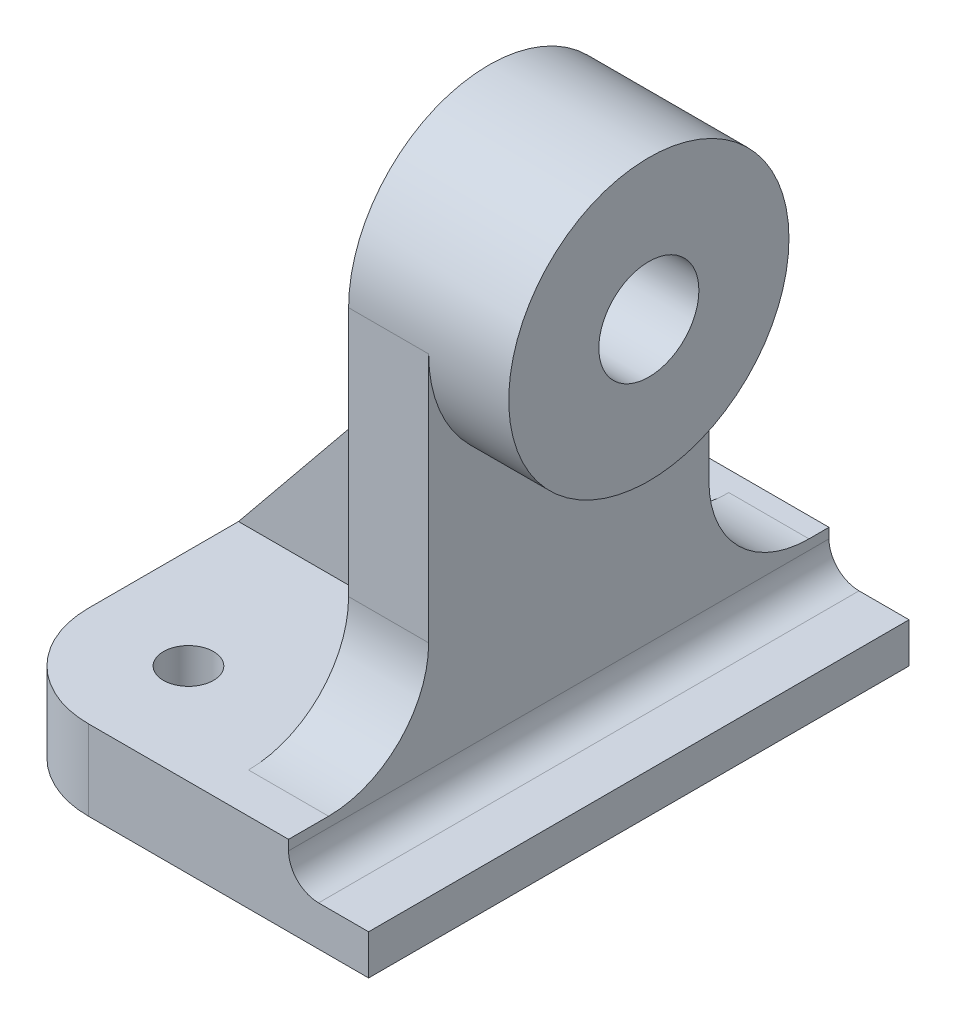
SolidWorks part; units mm, degrees
ref_plane "Ön Düzlem" through (0, 0, 0) normal (0, 0, 1) x (1, 0, 0)
ref_plane "Üst Düzlem" through (0, 0, 0) normal (0, 1, 0) x (1, 0, 0)
ref_plane "Sağ Düzlem" through (0, 0, 0) normal (1, 0, 0) x (0, 0, -1)
sketch "Çizim1" plane through (0, 0, 0) normal (0, 1, 0) x (1, 0, 0)
  line L1 (0, 0) -> (-38, 0)
  line L2 (0, 0) -> (0, 54)
  line L3 (0, 54) -> (-38, 54)
  line L4 (-38, 0) -> (-38, 54)
  dimension "D1" = 38
  dimension "D2" = 54
extrude "Yükseklik-Ekstrüzyon1" add sketch "Çizim1" along normal blind 8
sketch "Çizim2" plane through (0, 0, 0) normal (0, 0, 1) x (1, 0, 0)
  line L0 (0, 0) -> (0, 4) construction
  line L1 (0, 8) -> (0, 0) construction
  line L2 (0, 4) -> (-8, 4)
  line L3 (-8, 4) -> (-8, 8)
  line L4 (-38, 8) -> (0, 8) construction
  line L5 (-8, 8) -> (0, 8)
  line L6 (0, 8) -> (0, 4)
  dimension "D1" = 4
  dimension "D2" = 8
extrude "Kes-Ekstrüzyon1" cut sketch "Çizim2" against normal through all contours L6 L2 L3 L5
fillet "Radyus1" radius 3 1 edges at (-8, 4, -27)
ref_plane "Düzlem1" through (-8, 0, 0) normal (1, 0, 0) x (0, 0, -1)
fillet "Radyus2" radius 10 2 edges at (-38, 4, -54) (-38, 4, 0)
sketch "Çizim4" plane through (0, 8, 0) normal (0, 1, 0) x (1, 0, 0)
  circle A0 centre (-28, 44) radius 2.5
  circle A1 centre (-28, 10) radius 2.5
  arc A2 (-28, 54) -> (-38, 44) centre (-28, 44) ccw construction
  arc A3 (-38, 10) -> (-28, 0) centre (-28, 10) ccw construction
  dimension "D1" = 5
  dimension "D2" = 5
extrude "Kes-Ekstrüzyon2" cut sketch "Çizim4" against normal through all
sketch "Çizim5" plane through (-8, 0, 0) normal (1, 0, 0) x (0, 0, -1)
  line L0 (0, 0) -> (54, 0) construction
  line L2 (14, 43) -> (14, 8)
  line L3 (54, 8) -> (0, 8) construction
  line L4 (42, 43) -> (42, 8)
  line L5 (14, 8) -> (42, 8)
  line L6 (28, 8) -> (28, 43) construction
  arc A0 (42, 43) -> (14, 43) centre (28, 43) ccw
  dimension "D2" = 28
  dimension "D1" = 43
  dimension "D3" = 28
extrude "Yükseklik-Ekstrüzyon2" add sketch "Çizim5" against normal blind 8
fillet "Radyus3" radius 10 2 edges at (-12, 8, -42) (-12, 8, -14)
sketch "Çizim6" plane through (-8, 0, 0) normal (1, 0, 0) x (0, 0, -1)
  circle A0 centre (28, 43) radius 14
  dimension "D1" = 28
extrude "Yükseklik-Ekstrüzyon3" add sketch "Çizim6" along normal blind 8
sketch "Çizim7" plane through (0, 0, 0) normal (1, 0, 0) x (0, 0, -1)
  circle A0 centre (28, 43) radius 5
  dimension "D1" = 10
extrude "Kes-Ekstrüzyon3" cut sketch "Çizim7" against normal through all
ref_plane "Düzlem2" through (0, 0, -28) normal (0, 0, 1) x (1, 0, 0)
sketch "Çizim8" plane through (0, 0, -28) normal (0, 0, 1) x (1, 0, 0)
  line L2 (-16, 57) -> (-16, 43) construction
  line L5 (-38, 8) -> (-16, 35)
  line L6 (-16, 43) -> (-16, 18) construction
  point P7 (-16, 50)
  dimension "D1" = 3
rib "Feder2" sketch "Çizim8" sketch "Çizim8" thickness 6 extrusion direction parallel to sketch draft on no parameters "D1"=6
